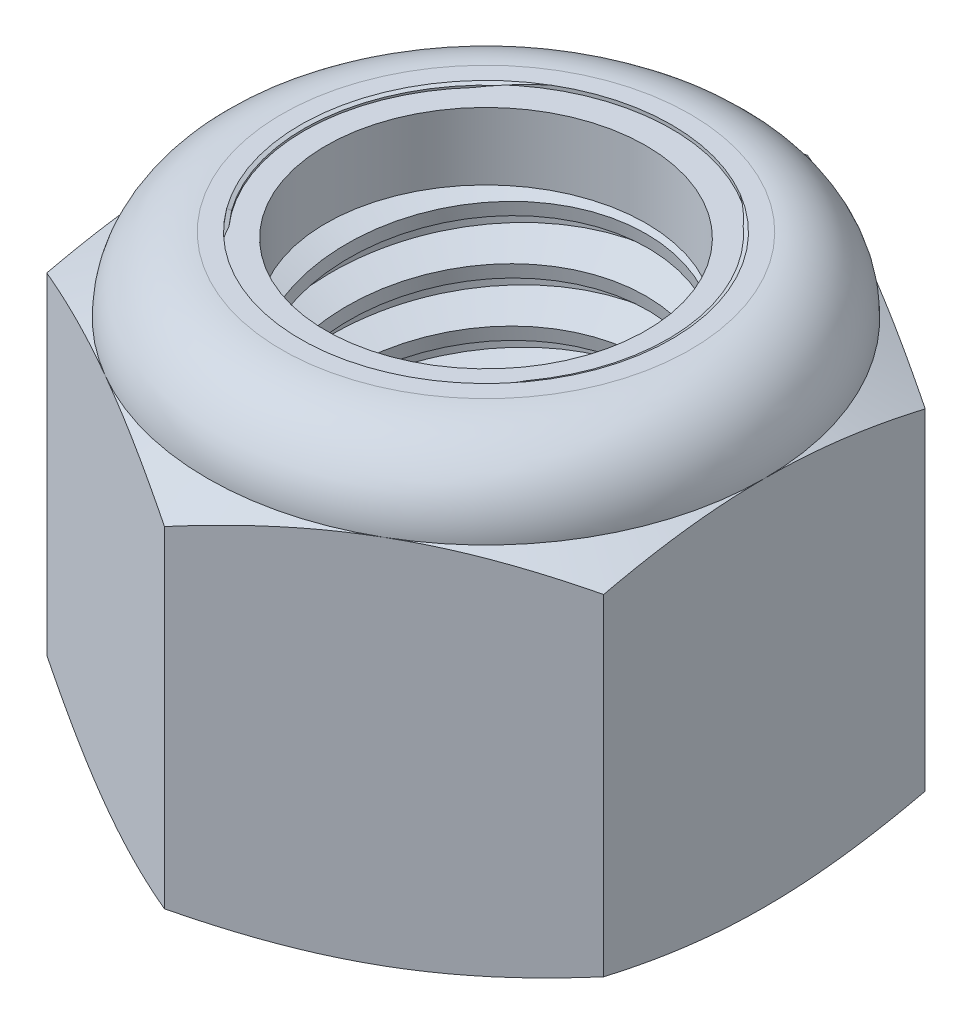
SolidWorks part; units mm, degrees
material "Plain Carbon Steel"
ref_plane "Front" through (0, 0, 0) normal (0, 0, 1) x (1, 0, 0)
ref_plane "Top" through (0, 0, 0) normal (0, 1, 0) x (1, 0, 0)
ref_plane "Right" through (0, 0, 0) normal (1, 0, 0) x (0, 0, -1)
sketch "Sketch1" plane through (0, 0, 0) normal (0, 1, 0) x (1, 0, 0)
  line L1 (0, 13.7482) -> (-11.9063, 6.8741)
  line L2 (-11.9063, 6.8741) -> (-11.9062, -6.8741)
  line L3 (-11.9062, -6.8741) -> (0, -13.7482)
  line L4 (0, -13.7482) -> (11.9062, -6.8741)
  line L5 (11.9062, -6.8741) -> (11.9062, 6.8741)
  line L6 (11.9062, 6.8741) -> (0, 13.7482)
  circle A0 centre (0, 0) radius 11.9063 construction
  dimension "Hex Flats" = 23.8125
extrude "Extrude1" add sketch "Sketch1" along normal blind 19.05
sketch "Sketch2" plane through (0, 0, 0) normal (1, 0, 0) x (0, 0, -1)
  line L0 (-7.9375, 0) -> (-7.9375, 19.05) construction
  line L1 (0, 0) -> (7.9375, 0)
  line L2 (0, 0) -> (0, 19.05)
  line L3 (0, 19.05) -> (7.9375, 19.05)
  line L4 (7.9375, 0) -> (7.9375, 19.05)
  line L5 (-6.8741, 19.05) -> (6.8741, 19.05) construction
  line L7 (0, -7.9375) -> (0, 0) construction
  dimension "Thread Dia" = 15.875
revolve "Revolve1" add sketch "Sketch2" angle 360 about L7
sketch "Sketch3" plane through (0, 0, 0) normal (1, 0, 0) x (0, 0, -1)
  line L0 (7.9375, 19.05) -> (-7.9375, 19.05) construction
  line L1 (-7.9375, 19.05) -> (-7.9375, 16.7409) construction
  line L2 (-7.9375, 16.7409) -> (7.9375, 19.05) construction
  line L3 (7.9375, 19.05) -> (7.979, 18.7644) construction
  line L4 (7.979, 18.7644) -> (8.2699, 16.765)
  line L5 (8.2699, 16.765) -> (6.9292, 17.2991)
  line L6 (6.9292, 17.2991) -> (6.8461, 17.8704)
  line L7 (6.8461, 17.8704) -> (7.979, 18.7644)
  line L8 (6.8876, 17.5848) -> (8.1245, 17.7647) construction
  line L9 (7.9375, 19.05) -> (7.9375, 17.7375) construction
  line L10 (7.9375, 17.7375) -> (-7.9375, 15.4284) construction
  line L11 (-7.9375, 15.4284) -> (-7.9375, 16.7409) construction
  line L12 (-0.3588, 19.05) -> (0.3588, 14.1158) construction
  line L13 (-7.9375, 0) -> (-7.9375, 19.05) construction
  line L14 (0, 19.05) -> (7.9375, 19.05) construction
  line L15 (7.9375, 0) -> (7.9375, 19.05) construction
  point P13 (0, 16.5829)
  dimension "D1" = 0.2886
  dimension "D2" = 0.5773
  dimension "Thread Pitch" = 2.3091
  dimension "D4" = 60
  dimension "D5" = 2.3091
revolve "Cut-Revolve1" cut sketch "Sketch3" angle 360 about L12
pattern_linear "LPattern1" count 8 spacing 2.3091 along (0, -1, 0) count 2 spacing 2.3091 along (0, 1, 0) of "Cut-Revolve1"
sketch "Sketch4" plane through (0, 0, 0) normal (1, 0, 0) x (0, 0, -1)
  line L0 (0, 19.05) -> (7.9375, 19.05)
  line L1 (7.9375, 19.05) -> (6.8461, 18.5411)
  line L2 (6.8461, 18.5411) -> (6.8461, 0.5089)
  line L3 (6.8461, 0.5089) -> (7.9375, 0)
  line L4 (7.9375, 0) -> (0, 0)
  line L5 (0, 0) -> (0, 19.05)
  line L6 (7.9375, 0) -> (7.9375, 19.05) construction
  line L7 (0, 19.05) -> (7.9375, 19.05) construction
  line L8 (0, 0) -> (7.9375, 0) construction
  line L9 (0, 0) -> (0, 19.05) construction
  line L10 (0, 19.05) -> (0, 20.2542) construction
  dimension "D1" = 25
revolve "Cut-Revolve2" cut sketch "Sketch4" angle 360 about L10
combine bodies "Combine1" operation type subtract main body 112 bodies to subtract 111
sketch "Sketch5" plane through (0, 0, 0) normal (1, 0, 0) x (0, 0, -1)
  line L0 (0, 0) -> (11.9063, 0)
  line L1 (11.9063, 0) -> (13.7482, 0.8589)
  line L2 (13.7482, 0.8589) -> (13.7482, 15.0161)
  line L3 (13.7482, 15.0161) -> (11.9063, 15.875)
  line L4 (8.7313, 19.05) -> (8.7313, 20.32)
  line L5 (8.7313, 20.32) -> (15.0182, 20.32)
  line L6 (15.0182, 20.32) -> (15.0182, -1.27)
  line L7 (15.0182, -1.27) -> (0, -1.27)
  line L8 (0, -1.27) -> (0, 0)
  line L9 (11.9063, 15.875) -> (11.9063, 0) construction
  line L10 (0, 0) -> (7.9375, 0) construction
  line L13 (13.7482, 7.9375) -> (15.0182, 7.9375) construction
  line L14 (13.7482, 19.05) -> (13.7482, 0) construction
  line L15 (0, 0) -> (0, 20.32) construction
  line L20 (0, 20.32) -> (8.7313, 20.32) construction
  line L22 (0, 19.05) -> (7.9375, 19.05) construction
  arc A0 (11.9063, 15.875) -> (8.7313, 19.05) centre (8.7313, 15.875) ccw
  dimension "D1" = 25
  dimension "D2" = 1.27
  dimension "D3" = 19.05
  dimension "D4" = 3.175
revolve "Cut-Revolve3" cut sketch "Sketch5" angle 360 about L15
sketch "Sketch6" plane through (0, 0, 0) normal (1, 0, 0) x (0, 0, -1)
  line L0 (0, 15.875) -> (11.7538, 15.875)
  line L1 (8.7313, 18.8976) -> (7.7887, 18.8976)
  line L2 (0, 20.32) -> (0, 15.875)
  line L3 (7.7887, 20.32) -> (0, 20.32)
  line L4 (0, 20.32) -> (8.7313, 20.32) construction
  line L5 (0, 0) -> (0, 20.32) construction
  line L6 (0, 20.32) -> (0, 44.323) construction
  line L7 (7.7887, 18.8976) -> (7.7887, 20.32)
  line L8 (8.7313, 19.05) -> (8.7313, 18.8976) construction
  line L9 (7.7887, 18.8976) -> (6.8461, 18.8976) construction
  line L10 (6.8461, 18.8976) -> (6.8461, 18.5411) construction
  arc A0 (11.7538, 15.875) -> (8.7313, 18.8976) centre (8.7313, 15.875) ccw
  arc A1 (11.9063, 15.875) -> (8.7313, 19.05) centre (8.7313, 15.875) ccw construction
  dimension "D1" = 0.1524
revolve "Cut-Revolve4" cut sketch "Sketch6" angle 360 about L6
sketch "Sketch7" plane through (0, 0, 0) normal (1, 0, 0) x (0, 0, -1)
  line L0 (6.8461, 15.9512) -> (11.6767, 15.9512)
  line L1 (8.7313, 18.8214) -> (6.8461, 18.8214)
  line L2 (6.8461, 18.8214) -> (6.8461, 15.9512)
  line L3 (6.8461, 15.9512) -> (0, 15.9512) construction
  line L4 (0, 15.9512) -> (0, 18.8214) construction
  line L5 (0, 18.8214) -> (6.8461, 18.8214) construction
  line L6 (6.8461, 15.9512) -> (6.8461, 15.875) construction
  line L7 (0, 15.875) -> (11.7538, 15.875) construction
  line L8 (8.7313, 18.8214) -> (8.7313, 18.8976) construction
  arc A0 (11.6767, 15.9512) -> (8.7313, 18.8214) centre (8.7313, 15.875) ccw
  arc A2 (11.7538, 15.875) -> (8.7313, 18.8976) centre (8.7313, 15.875) ccw construction
  dimension "D1" = 0.0762
revolve "Revolve2" add sketch "Sketch7" angle 360 about L4
equation "\"D1@Sketch3\"=\"Thread Pitch@Sketch3\"/8"
equation "\"D2@Sketch3\"=\"Thread Pitch@Sketch3\"/4"
equation "\"D5@Sketch3\"=\"Thread Pitch@Sketch3\""
equation "\"D4@LPattern1\"=\"Thread Pitch@Sketch3\""
equation "\"D3@LPattern1\"=\"Thread Pitch@Sketch3\""
equation "\"D1@LPattern1\"=\"Height@Extrude1\"/\"Thread Pitch@Sketch3\""
equation "\"D4@Sketch5\"=\"Height@Extrude1\"/6"
